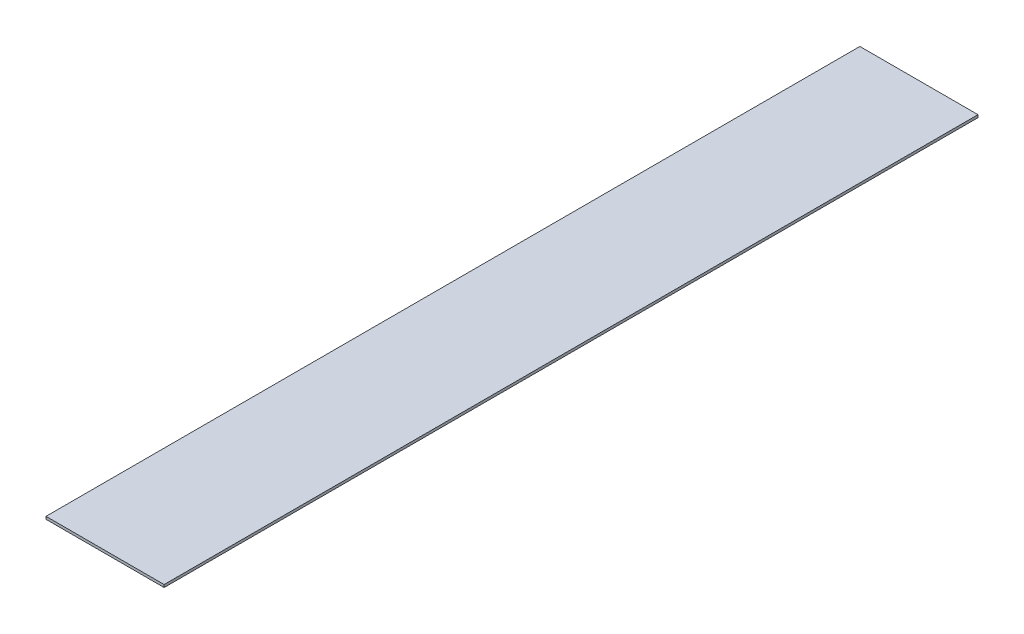
SolidWorks part; units mm, degrees
ref_plane "前视基准面" through (0, 0, 0) normal (0, 0, 1) x (1, 0, 0)
ref_plane "上视基准面" through (0, 0, 0) normal (0, 1, 0) x (1, 0, 0)
ref_plane "右视基准面" through (0, 0, 0) normal (1, 0, 0) x (0, 0, -1)
sketch "Sketch1" plane through (0, 0, 0) normal (0, 1, 0) x (1, 0, 0)
  line L1 (-45, 310) -> (45, 310)
  line L2 (-45, 310) -> (-45, -310)
  line L3 (-45, -310) -> (45, -310)
  line L4 (45, 310) -> (45, -310)
  line L5 (-45, 310) -> (45, -310) construction
  line L6 (-45, -310) -> (45, 310) construction
  point P0 (0, 0)
  dimension "D1" = 90
  dimension "620" = 620
extrude "Boss-Extrude1" add sketch "Sketch1" along normal blind 2
